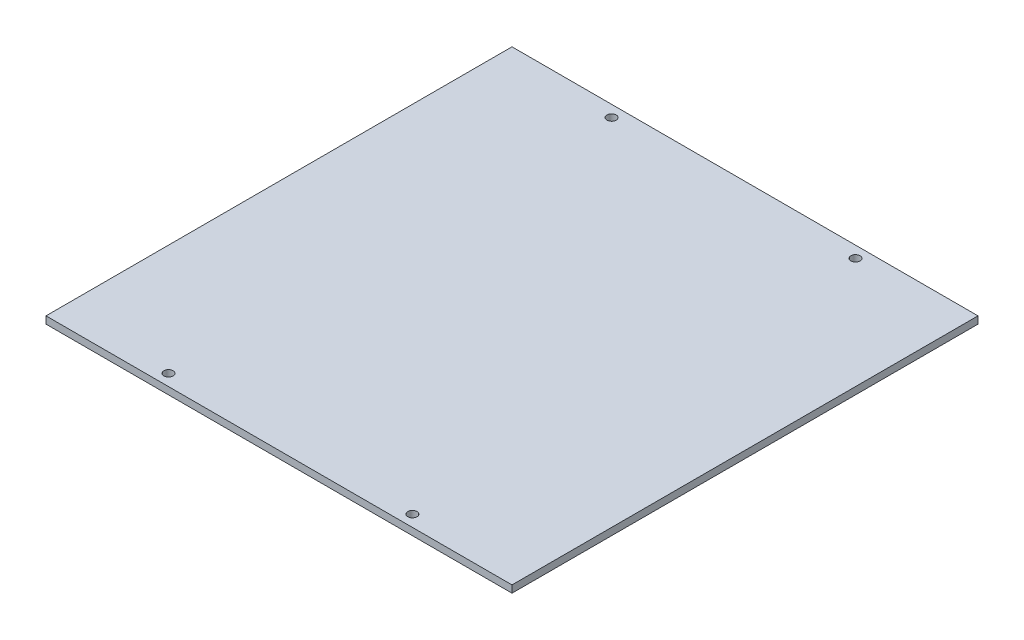
SolidWorks part; units mm, degrees
ref_plane "Front Plane" through (0, 0, 0) normal (0, 0, 1) x (1, 0, 0)
ref_plane "Top Plane" through (0, 0, 0) normal (0, 1, 0) x (1, 0, 0)
ref_plane "Right Plane" through (0, 0, 0) normal (1, 0, 0) x (0, 0, -1)
sketch "Sketch1" plane through (0, 0, 0) normal (0, 1, 0) x (1, 0, 0)
  line L1 (50.8, -50.8) -> (-50.8, -50.8)
  line L2 (50.8, -50.8) -> (50.8, 50.8)
  line L3 (50.8, 50.8) -> (-50.8, 50.8)
  line L4 (-50.8, -50.8) -> (-50.8, 50.8)
  line L5 (50.8, -50.8) -> (-50.8, 50.8) construction
  line L6 (50.8, 50.8) -> (-50.8, -50.8) construction
  line L7 (26.5875, -48.3) -> (-26.5875, -48.3) construction
  line L8 (26.5875, -48.3) -> (26.5875, 48.3) construction
  line L9 (26.5875, 48.3) -> (-26.5875, 48.3) construction
  line L10 (-26.5875, -48.3) -> (-26.5875, 48.3) construction
  line L11 (26.5875, -48.3) -> (-26.5875, 48.3) construction
  line L12 (26.5875, 48.3) -> (-26.5875, -48.3) construction
  circle A0 centre (-26.5875, -48.3) radius 1
  circle A1 centre (-26.5875, 48.3) radius 1
  circle A2 centre (26.5875, 48.3) radius 1
  circle A3 centre (26.5875, -48.3) radius 1
  point P0 (0, 0)
  point P6 (0, 0)
  dimension "D3" = 2
  dimension "D1" = 101.6
  dimension "D2" = 101.6
  dimension "D4" = 53.175
  dimension "D5" = 2.5
extrude "Boss-Extrude1" add sketch "Sketch1" along normal blind 1.57
